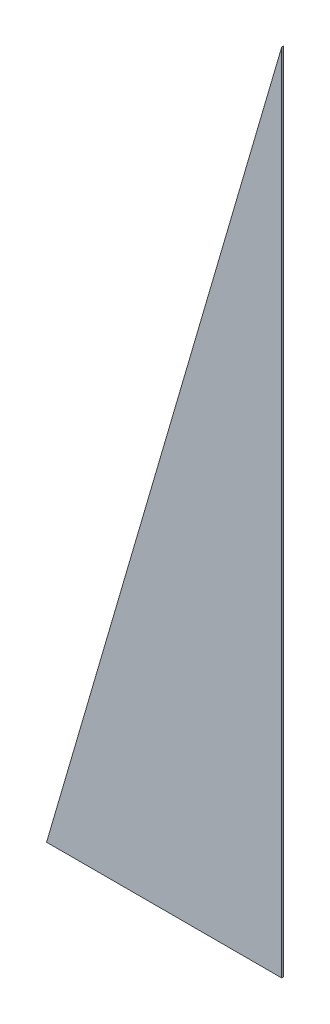
SolidWorks part; units mm, degrees
ref_plane "Front Plane" through (0, 0, 0) normal (0, 0, 1) x (1, 0, 0)
ref_plane "Top Plane" through (0, 0, 0) normal (0, 1, 0) x (1, 0, 0)
ref_plane "Right Plane" through (0, 0, 0) normal (1, 0, 0) x (0, 0, -1)
sketch "Sketch1" plane through (0, 0, 0) normal (0, 0, 1) x (1, 0, 0)
  line L0 (0, 0) -> (0, 1219.2)
  line L1 (0, 1219.2) -> (-355.6, 0)
  line L2 (-355.6, 0) -> (0, 0)
  dimension "D1" = 1219.2
  dimension "D2" = 355.6
extrude "Boss-Extrude1" add sketch "Sketch1" along normal blind 2.54
